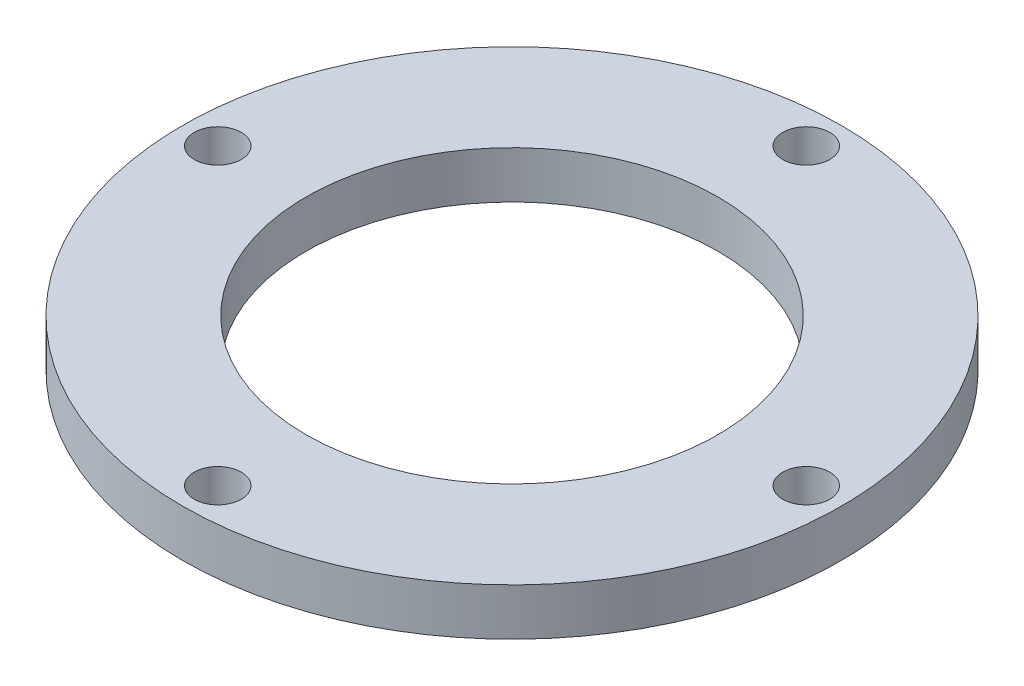
SolidWorks part; units mm, degrees
material "Acier non allié"
ref_plane "Plan de face" through (0, 0, 0) normal (0, 0, 1) x (1, 0, 0)
ref_plane "Plan de dessus" through (0, 0, 0) normal (0, 1, 0) x (1, 0, 0)
ref_plane "Plan de droite" through (0, 0, 0) normal (1, 0, 0) x (0, 0, -1)
sketch "Esquisse1" plane through (0, 0, 0) normal (0, 1, 0) x (1, 0, 0)
  circle A0 centre (0, 0) radius 56
  circle A1 centre (0, 0) radius 35
  circle A2 centre (0, 50) radius 4
  circle A3 centre (50, 0) radius 4
  circle A4 centre (0, -50) radius 4
  circle A5 centre (-50, 0) radius 4
  point P15 (0, 0)
  dimension "D1" = 70
  dimension "D2" = 112
  dimension "D3" = 50
  dimension "D4" = 4
extrude "Boss.-Extru.1" add sketch "Esquisse1" along normal blind 8
